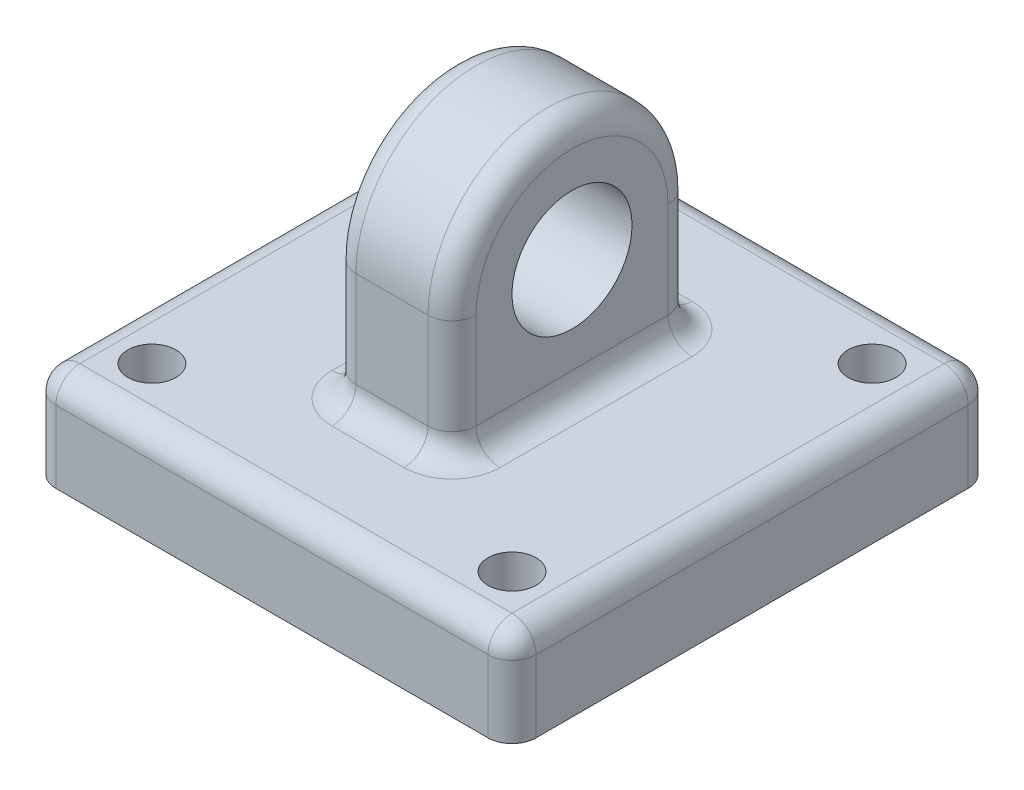
SolidWorks part; units mm, degrees
ref_plane "Plan de face" through (0, 0, 0) normal (0, 0, 1) x (1, 0, 0)
ref_plane "Plan de dessus" through (0, 0, 0) normal (0, 1, 0) x (1, 0, 0)
ref_plane "Plan de droite" through (0, 0, 0) normal (1, 0, 0) x (0, 0, -1)
sketch "Esquisse2" plane through (0, 0, 0) normal (1, 0, 0) x (0, 0, -1)
  line L0 (5, 0) -> (5, -5)
  line L2 (-5, 0) -> (-5, -5)
  line L3 (-5, -5) -> (5, -5)
  circle A0 centre (0, 0) radius 2.5
  arc A2 (5, 0) -> (-5, 0) centre (0, 0) ccw
  dimension "D1" = 5
  dimension "D2" = 5
  dimension "D3" = 5
  dimension "D4" = 5
extrude "Boss.-Extru.1" add sketch "Esquisse2" along normal mid plane 5
sketch "Esquisse4" plane through (0, -5, 0) normal (0, -1, 0) x (1, 0, 0)
  line L1 (-10, -10) -> (10, -10)
  line L2 (-10, -10) -> (-10, 10)
  line L3 (-10, 10) -> (10, 10)
  line L4 (10, -10) -> (10, 10)
  point P7 (-0.2341, -3.5641)
  dimension "D1" = 20
  dimension "D2" = 20
  dimension "D3" = 10
  dimension "D4" = 10
extrude "Boss.-Extru.2" add sketch "Esquisse4" along normal blind 4
sketch "Esquisse5" plane through (0, -5, 0) normal (0, 1, 0) x (1, 0, 0)
  circle A0 centre (7.5, -7.5) radius 1
  circle A1 centre (7.5, 7.5) radius 1
  circle A2 centre (-7.5, 7.5) radius 1
  circle A3 centre (-7.5, -7.5) radius 1
  point P15 (0, 0)
  dimension "D1" = 2
  dimension "D2" = 15
  dimension "D3" = 15
  dimension "D4" = 7.5
  dimension "D5" = 7.5
extrude "Enlèv. mat.-Extru.1" cut sketch "Esquisse5" against normal up to next contours A0
fillet "Congé1" radius 1 18 edges at (10, -7, 10) (-10, -7, 10) (-10, -7, -10) (10, -7, -10) (0, -5, -10) (-10, -5, 0) (0, -5, 10) (10, -5, 0) (0, -5, -5) (2.5, -5, 0) (-2.5, -5, 0) (-2.5, -2.5, -5) (-2.5, 5, 0) (2.5, -2.5, -5) (2.5, 5, 0) (0, -5, 5) (-2.5, -2.5, 5) (2.5, -2.5, 5)
